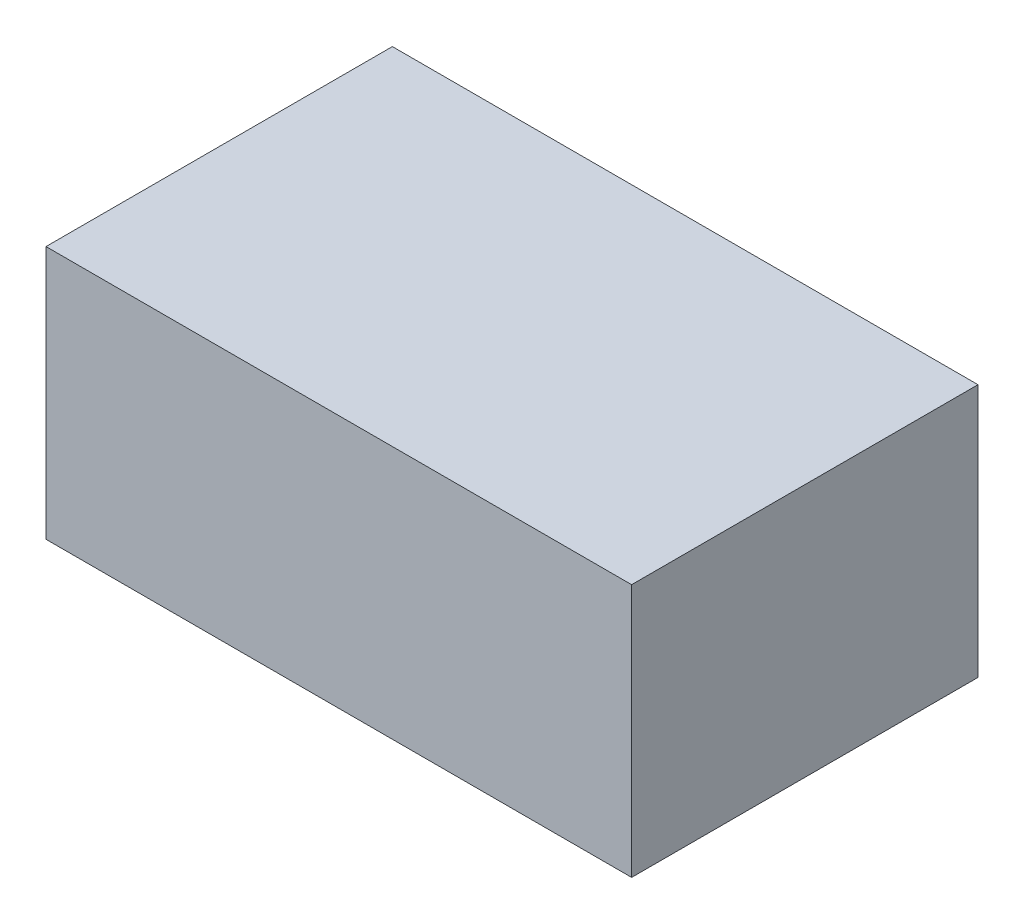
SolidWorks part; units mm, degrees
ref_plane "Front Plane" through (0, 0, 0) normal (0, 0, 1) x (1, 0, 0)
ref_plane "Top Plane" through (0, 0, 0) normal (0, 1, 0) x (1, 0, 0)
ref_plane "Right Plane" through (0, 0, 0) normal (1, 0, 0) x (0, 0, -1)
sketch "Sketch1" plane through (0, 0, 0) normal (0, 1, 0) x (1, 0, 0)
  line L1 (0, 0) -> (984, 0)
  line L2 (0, 0) -> (0, 582)
  line L3 (0, 582) -> (984, 582)
  line L4 (984, 0) -> (984, 582)
  dimension "D1" = 984
  dimension "D2" = 582
extrude "Extrude1" add sketch "Sketch1" along normal blind 426
